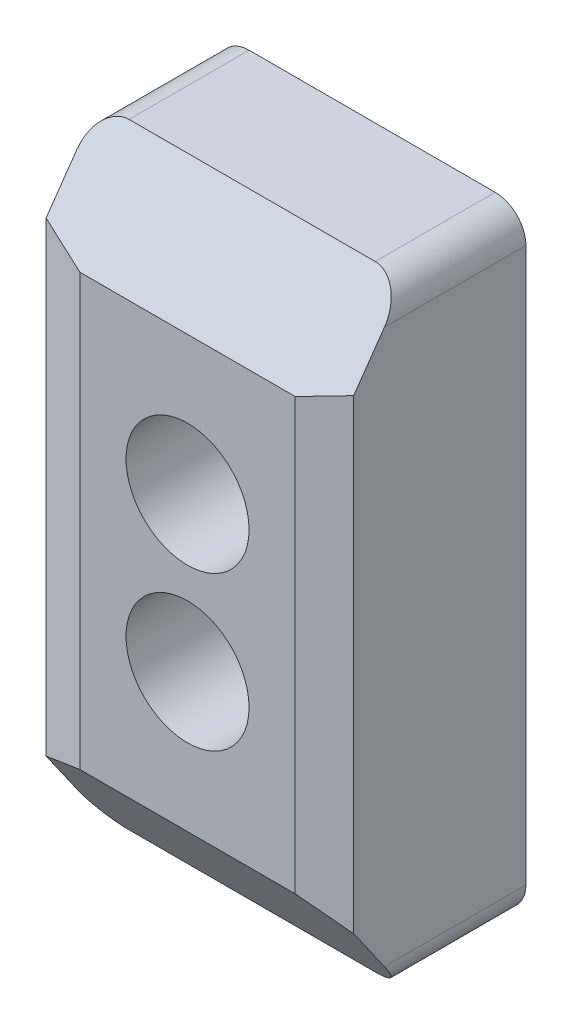
SolidWorks part; units mm, degrees
ref_plane "Front Plane" through (0, 0, 0) normal (0, 0, 1) x (1, 0, 0)
ref_plane "Top Plane" through (0, 0, 0) normal (0, 1, 0) x (1, 0, 0)
ref_plane "Right Plane" through (0, 0, 0) normal (1, 0, 0) x (0, 0, -1)
sketch "Sketch1" plane through (0, 0, 0) normal (0, 0, 1) x (1, 0, 0)
  line L0 (-10, -20) -> (-10, 20)
  line L1 (-10, -20) -> (10, -20)
  line L2 (-10, 20) -> (10, 20)
  line L3 (10, -20) -> (10, 20)
  line L4 (-10, -20) -> (10, 20) construction
  line L5 (-10, 20) -> (10, -20) construction
  line L6 (0, 5) -> (0, -5) construction
  circle A0 centre (0, -5) radius 2.15
  circle A1 centre (0, 5) radius 2.15
  point P1 (0, 0)
  point P22 (0, 0)
  dimension "D4" = 10
  dimension "D5" = 4.3
  dimension "D1" = 40
  dimension "D2" = 20
extrude "Boss-Extrude1" add sketch "Sketch1" along normal blind 12
chamfer "Chamfer1" distance 3 angle 15 2 edges at (10, 0, 12) (-10, 0, 12)
chamfer "Chamfer2" distance 6 angle 35 2 edges at (0, -20, 12) (0, 20, 12)
sketch "Sketch2" plane through (0, 0, 12) normal (0, 0, 1) x (1, 0, 0)
  circle A0 centre (0, 5) radius 4
  circle A1 centre (0, -5) radius 4
  dimension "D1" = 8
extrude "Cut-Extrude1" cut sketch "Sketch2" against normal offset from surface (11 mm away) 1 up to face at (2.15, -5, 0)
fillet "Fillet1" radius 2 4 edges at (-10, 20, 3.8994) (10, 20, 3.8994) (-10, -20, 3.8994) (10, -20, 3.8994)
